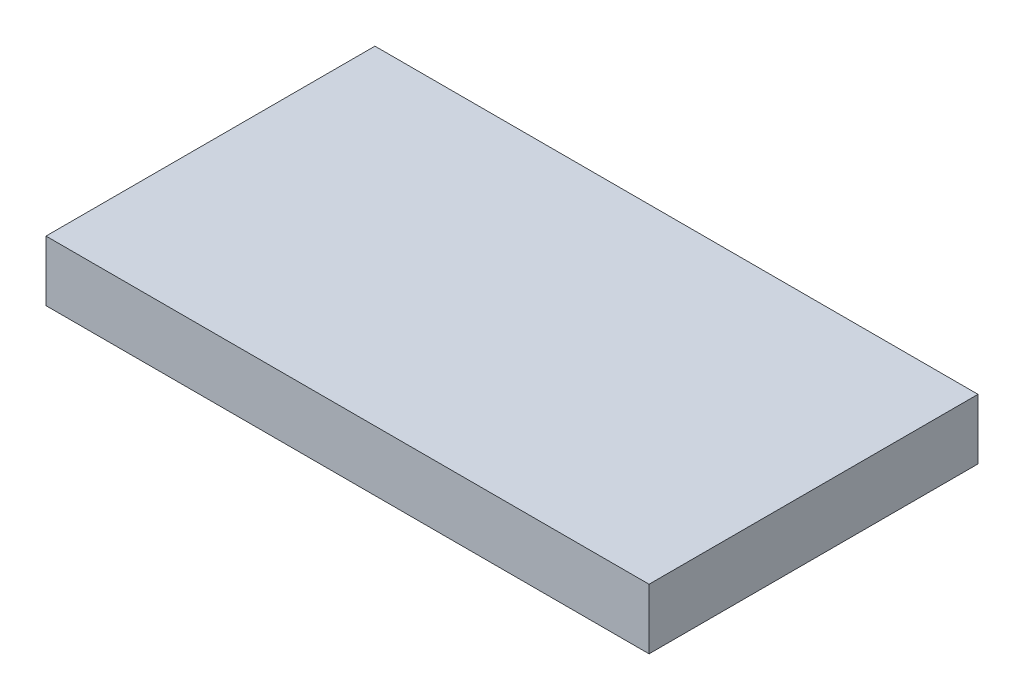
SolidWorks part; units mm, degrees
ref_plane "Front Plane" through (0, 0, 0) normal (0, 0, 1) x (1, 0, 0)
ref_plane "Top Plane" through (0, 0, 0) normal (0, 1, 0) x (1, 0, 0)
ref_plane "Right Plane" through (0, 0, 0) normal (1, 0, 0) x (0, 0, -1)
sketch "Sketch1" plane through (0, 0, 0) normal (0, 1, 0) x (1, 0, 0)
  line L1 (-8.25, -4.5) -> (8.25, -4.5)
  line L2 (-8.25, -4.5) -> (-8.25, 4.5)
  line L3 (-8.25, 4.5) -> (8.25, 4.5)
  line L4 (8.25, -4.5) -> (8.25, 4.5)
  line L5 (-8.25, -4.5) -> (8.25, 4.5) construction
  line L6 (-8.25, 4.5) -> (8.25, -4.5) construction
  point P0 (0, 0)
  dimension "D1" = 9
  dimension "D2" = 16.5
extrude "Boss-Extrude1" add sketch "Sketch1" along normal blind 1.65
